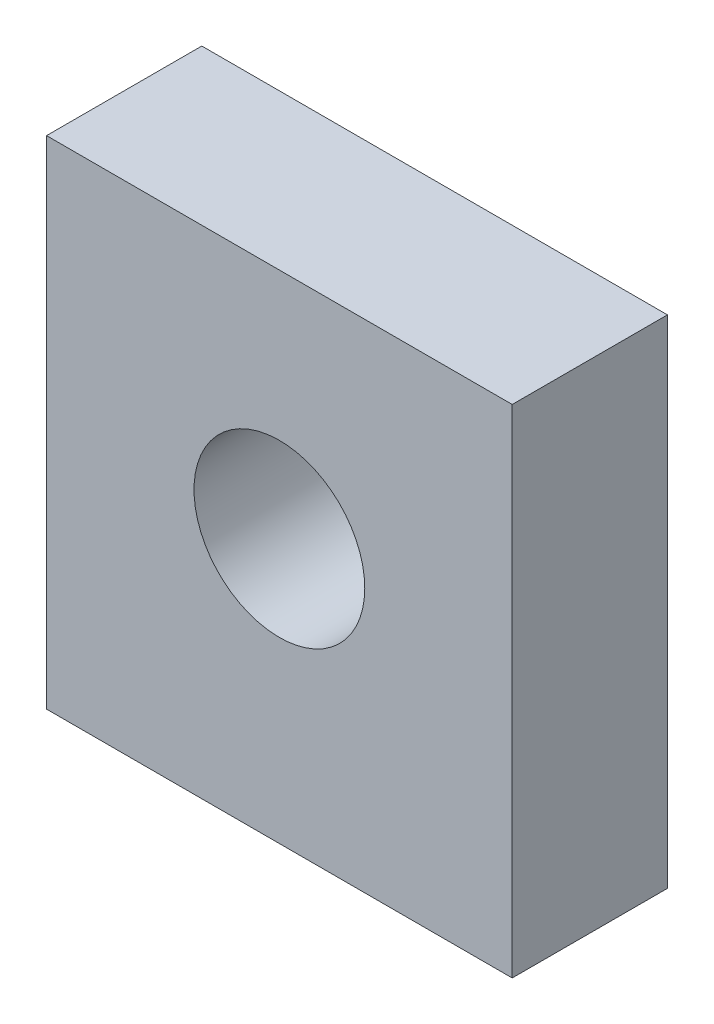
SolidWorks part; units mm, degrees
material "6061 Alloy"
ref_plane "Front Plane" through (0, 0, 0) normal (0, 0, 1) x (1, 0, 0)
ref_plane "Top Plane" through (0, 0, 0) normal (0, 1, 0) x (1, 0, 0)
ref_plane "Right Plane" through (0, 0, 0) normal (1, 0, 0) x (0, 0, -1)
sketch "Sketch1" plane through (0, 0, 0) normal (1, 0, 0) x (0, 0, -1)
  line L1 (0, 0) -> (10, 0)
  line L2 (0, 0) -> (0, 32)
  line L3 (0, 32) -> (10, 32)
  line L4 (10, 0) -> (10, 32)
  dimension "D1" = 32
  dimension "D2" = 10
extrude "Boss-Extrude1" add sketch "Sketch1" along normal blind 30
hole_wizard "M4 Tapped Hole1" positions "Sketch2" profile "Sketch3" tap size "M4" standard "ISO"
sketch "Sketch2" plane through (0, 0, 0) normal (0, -1, 0) x (-1, 0, 0)
  line L0 (0, 0) -> (0, 10) construction
  line L1 (-30, 0) -> (-30, 10) construction
  point P0 (-5, 5)
  point P2 (-25, 5)
  point P10 (0, 5)
  dimension "D1" = 5
  dimension "D2" = 5
sketch "Sketch3" plane through (5, 0, -5) normal (1, 0, 0) x (0, 0, -1)
  line L0 (0, 0) -> (0, 11.0914)
  line L1 (0, 11.0914) -> (1.65, 10.1)
  line L2 (1.65, 10.1) -> (1.65, 0)
  line L5 (1.65, 0) -> (0, 0)
  line L10 (0, 11.0914) -> (-1.65, 10.1) construction
  line L11 (0, -6.35) -> (0, 107.95) construction
  dimension "Tap Drill Dia." = 3.3
  dimension "Tap Drill Depth" = 10.1
  dimension "Drill Angle" = 118
cosmetic thread "Hole Thread1" parameters "D1"=8, "D2"=4
cosmetic thread "Hole Thread2" parameters "D1"=8, "D2"=4
sketch "Sketch4" plane through (0, 0, 0) normal (0, 0, 1) x (1, 0, 0)
  line L0 (30, 0) -> (0, 0) construction
  circle A0 centre (15, 17) radius 5.5
  point P5 (15, 0)
  dimension "D2" = 11
  dimension "D1" = 17
extrude "Cut-Extrude2" cut sketch "Sketch4" against normal blind 10
